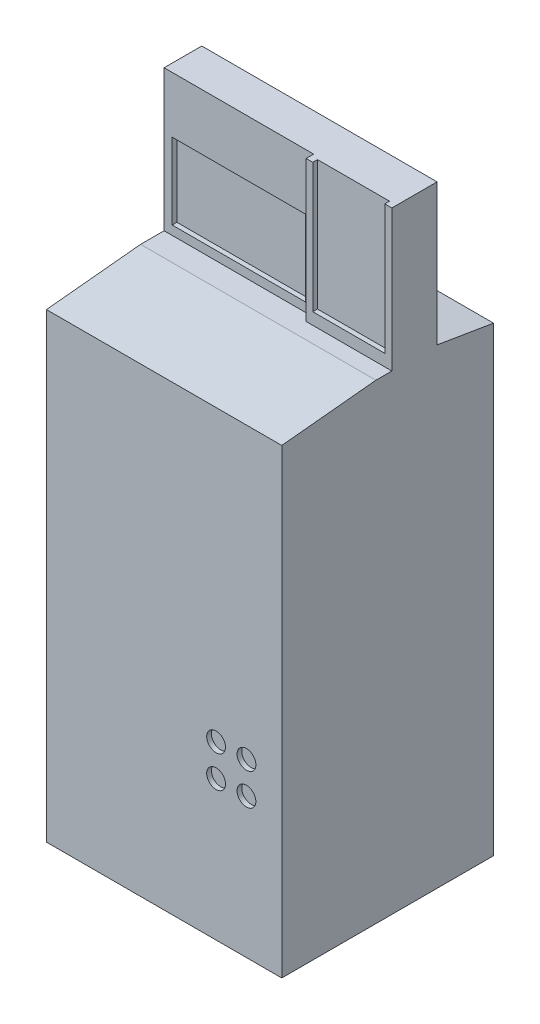
SolidWorks part; units mm, degrees
ref_plane "Front Plane" through (0, 0, 0) normal (0, 0, 1) x (1, 0, 0)
ref_plane "Top Plane" through (0, 0, 0) normal (0, 1, 0) x (1, 0, 0)
ref_plane "Right Plane" through (0, 0, 0) normal (1, 0, 0) x (0, 0, -1)
sketch "Sketch2" plane through (0, 0, 0) normal (0, 1, 0) x (1, 0, 0)
  line L1 (-250, -225) -> (250, -225)
  line L2 (-250, -225) -> (-250, 225)
  line L3 (-250, 225) -> (250, 225)
  line L4 (250, -225) -> (250, 225)
  line L5 (-250, -225) -> (250, 225) construction
  line L6 (-250, 225) -> (250, -225) construction
  point P0 (0, 0)
  dimension "D1" = 500
  dimension "D2" = 450
extrude "Boss-Extrude1" add sketch "Sketch2" along normal blind 800 and the other way blind 200
chamfer "Chamfer1" distance 20 distance2 200 1 edges at (0, 800, 225)
chamfer "Chamfer2" distance 20 distance2 120 1 edges at (0, 800, -225)
sketch "Sketch9" plane through (0, 800, 0) normal (0, 1, 0) x (1, 0, 0)
  line L0 (250, -25) -> (250, 105) construction
  line L1 (-250, 105) -> (250, 105)
  line L2 (-250, 105) -> (-250, 8.908)
  line L3 (-250, 8.908) -> (250, 8.908)
  line L4 (250, 105) -> (250, 8.908)
  line L6 (-250, 105) -> (67.8161, 105)
  line L7 (-250, 105) -> (-250, 25)
  line L8 (-250, 25) -> (67.8161, 25)
  line L9 (67.8161, 105) -> (67.8161, 25)
  line L10 (67.8161, 105) -> (250, 105)
  line L11 (67.8161, 105) -> (67.8161, 8.908)
  line L12 (67.8161, 8.908) -> (250, 8.908)
  line L13 (250, 105) -> (250, 8.908)
  line M1 (250, -25) -> (250, 105)
  line M2 (250, 105) -> (-250, 105)
  line M3 (-250, 105) -> (-250, -25)
extrude "Boss-Extrude2" add sketch "Sketch9" along normal blind 300 contours L9 L1 L8 M3 | L9 L11 L3 M1 M2
sketch "Sketch10" plane through (0, 0, -25) normal (0, 0, 1) x (1, 0, 0)
  line L1 (-250, 1100) -> (67.8161, 1100)
  line L2 (-250, 1100) -> (-250, 800)
  line L3 (-250, 800) -> (67.8161, 800)
  line L4 (67.8161, 1100) -> (67.8161, 800)
  line L5 (-232.8179, 819.1857) -> (50.634, 819.1857)
  line L6 (-232.8179, 819.1857) -> (-232.8179, 980.8143)
  line L7 (-232.8179, 980.8143) -> (50.634, 980.8143)
  line L8 (50.634, 819.1857) -> (50.634, 980.8143)
  line L9 (-232.8179, 819.1857) -> (50.634, 980.8143) construction
  line L10 (-232.8179, 980.8143) -> (50.634, 819.1857) construction
  point P6 (-91.092, 900)
extrude "Cut-Extrude1" cut sketch "Sketch10" against normal blind 10 contours L5 L8 L7 L6
sketch "Sketch11" plane through (0, 0, 225) normal (0, 0, 1) x (1, 0, 0)
  line L1 (0, 393.3589) -> (220.9449, 393.3589)
  line L2 (0, 393.3589) -> (0, 33.2059)
  line L3 (0, 33.2059) -> (220.9449, 33.2059)
  line L4 (220.9449, 393.3589) -> (220.9449, 33.2059)
  circle A0 centre (110.4725, 164.7512) radius 20
  circle A1 centre (174.968, 164.7512) radius 20
  circle A2 centre (110.4725, 97.0628) radius 20
  circle A3 centre (174.968, 97.0628) radius 20
  dimension "D1" = 40
  dimension "D2" = 40
  dimension "D3" = 40
  dimension "D4" = 40
extrude "Cut-Extrude2" cut sketch "Sketch11" against normal blind 10 contours A0 | A1 | A2 | A3
sketch "Sketch12" plane through (0, 0, -8.908) normal (0, 0, 1) x (1, 0, 0)
  line L0 (67.8161, 1100) -> (250, 1100) construction
  line L1 (81.9672, 1100) -> (234.9649, 1100)
  line L2 (81.9672, 1100) -> (81.9672, 825.0451)
  line L3 (81.9672, 825.0451) -> (234.9649, 825.0451)
  line L4 (234.9649, 1100) -> (234.9649, 825.0451)
extrude "Cut-Extrude3" cut sketch "Sketch12" against normal blind 10
sketch "Sketch13" plane through (0, 825.0451, 0) normal (0, 1, 0) x (1, 0, 0)
  line L0 (250, 105) -> (-250, 105) construction
  line L1 (234.9649, 105) -> (81.9672, 105)
  line L2 (234.9649, 105) -> (234.9649, 87.1109)
  line L3 (234.9649, 87.1109) -> (81.9672, 87.1109)
  line L4 (81.9672, 105) -> (81.9672, 87.1109)
  line L5 (81.9672, 18.908) -> (81.9672, 8.908) construction
extrude "Boss-Extrude3" add sketch "Sketch13" along normal blind 175
sketch "Sketch15" plane through (0, 0, -225) normal (0, 0, -1) x (-1, 0, 0)
  line L1 (-201.0984, 108.6057) -> (201.2015, 108.6057)
  line L2 (-201.0984, 108.6057) -> (-201.0984, -164.043)
  line L3 (-201.0984, -164.043) -> (201.2015, -164.043)
  line L4 (201.2015, 108.6057) -> (201.2015, -164.043)
extrude "Cut-Extrude4" cut sketch "Sketch15" against normal blind 70
